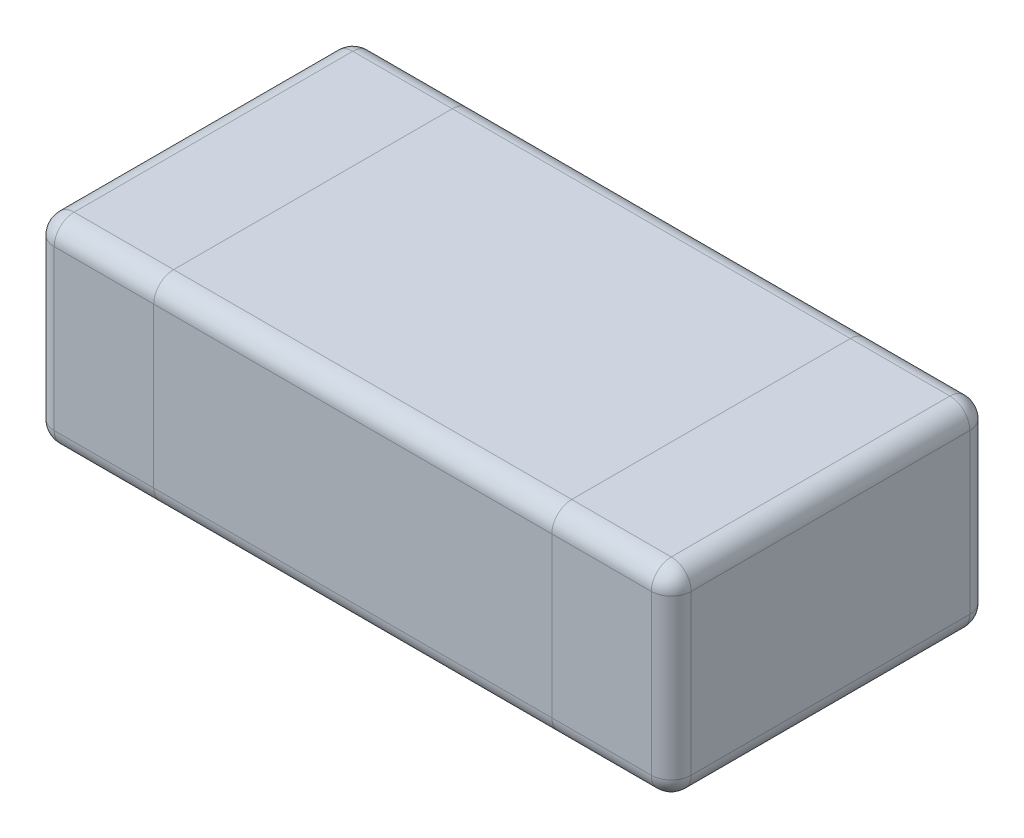
SolidWorks part; units mm, degrees
ref_plane "Front Plane" through (0, 0, 0) normal (0, 0, 1) x (1, 0, 0)
ref_plane "Top Plane" through (0, 0, 0) normal (0, 1, 0) x (1, 0, 0)
ref_plane "Right Plane" through (0, 0, 0) normal (1, 0, 0) x (0, 0, -1)
sketch "Sketch1" plane through (0, 0, 0) normal (0, 1, 0) x (1, 0, 0)
  line L1 (0, 0) -> (0.3, 0)
  line L2 (0, 0) -> (0, 0.8)
  line L3 (0, 0.8) -> (0.3, 0.8)
  line L4 (0.3, 0) -> (0.3, 0.8)
  line L5 (0.15, 0.8) -> (0.15, 0) construction
  line L6 (0, 0.4) -> (0.3, 0.4) construction
  line L7 (1.3, 0.8) -> (1.6, 0.8)
  line L8 (1.3, 0.8) -> (1.3, 0)
  line L9 (1.3, 0) -> (1.6, 0)
  line L10 (1.6, 0.8) -> (1.6, 0)
  line L11 (1.45, 0) -> (1.45, 0.8) construction
  line L12 (1.3, 0.4) -> (1.6, 0.4) construction
  point P112 (0.15, 0.4)
  point P158 (1.45, 0.4)
  dimension "D1" = 0.8
  dimension "D2" = 0.8
  dimension "D3" = 1.6
  dimension "D4" = 0.3
  dimension "D5" = 0.3
extrude "Boss-Extrude1" add sketch "Sketch1" along normal blind 0.5
sketch "Sketch2" plane through (0, 0, 0) normal (0, 1, 0) x (1, 0, 0)
  line L1 (0.3, 0.8) -> (1.3, 0.8)
  line L2 (0.3, 0.8) -> (0.3, 0)
  line L3 (0.3, 0) -> (1.3, 0)
  line L4 (1.3, 0.8) -> (1.3, 0)
  line L5 (0.8, 0) -> (0.8, 0.8) construction
  line L6 (0.3, 0.4) -> (1.3, 0.4) construction
  point P132 (0.8, 0.4)
extrude "Boss-Extrude2" add sketch "Sketch2" along normal blind 0.5 separate body
sketch "Sketch3" plane through (0, 0.5, 0) normal (0, 1, 0) x (1, 0, 0)
  line L0 (0.3, 0) -> (1.3, 0) construction
  line L1 (0, 0.8) -> (0, 0) construction
  point P0 (0.8, 0.4)
  dimension "D1" = 0.4
  dimension "D2" = 0.8
fillet "Fillet1" radius 0.05 8 edges at (0, 0.25, -0.8) (0, 0.5, -0.4) (0, 0.25, 0) (0, 0, -0.4) (0.15, 0, -0.8) (0.15, 0, 0) (0.15, 0.5, -0.8) (0.15, 0.5, 0)
fillet "Fillet2" radius 0.05 8 edges at (1.6, 0.25, 0) (1.6, 0.5, -0.4) (1.6, 0.25, -0.8) (1.6, 0, -0.4) (1.45, 0, 0) (1.45, 0.5, 0) (1.45, 0, -0.8) (1.45, 0.5, -0.8)
fillet "Fillet3" radius 0.05 4 edges at (0.8, 0, 0) (0.8, 0, -0.8) (0.8, 0.5, -0.8) (0.8, 0.5, 0)
